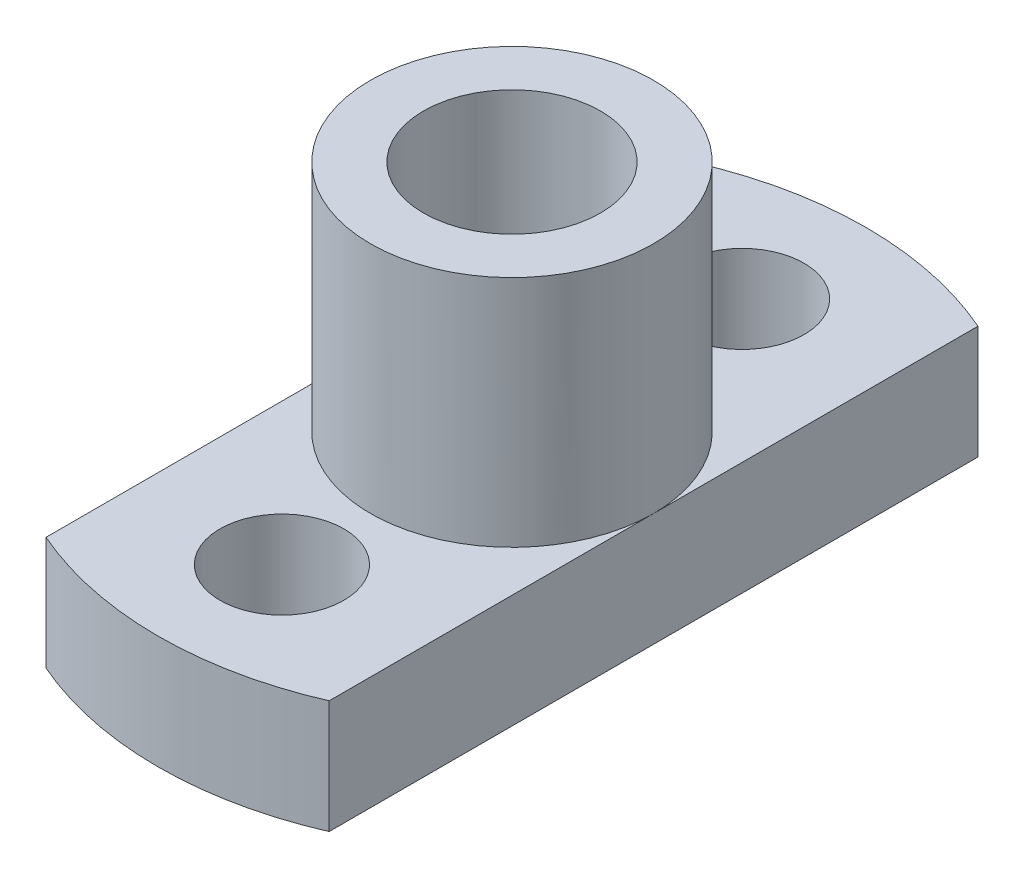
SolidWorks part; units mm, degrees
ref_plane "前视基准面" through (0, 0, 0) normal (0, 0, 1) x (1, 0, 0)
ref_plane "上视基准面" through (0, 0, 0) normal (0, 1, 0) x (1, 0, 0)
ref_plane "右视基准面" through (0, 0, 0) normal (1, 0, 0) x (0, 0, -1)
sketch "草图2" plane through (0, 0, 0) normal (0, 1, 0) x (1, 0, 0)
  line L0 (0, 10) -> (0, -10) construction
  line L1 (-4, 9.1652) -> (-4, -9.1652)
  line L2 (4, 9.1652) -> (4, -9.1652)
  line L3 (-4, 0) -> (4, 0) construction
  arc A0 (-4, -9.1652) -> (4, -9.1652) centre (0, 0) ccw
  arc A1 (4, 9.1652) -> (-4, 9.1652) centre (0, 0) ccw
  circle A3 centre (0, 6.5) radius 1.75
  circle A4 centre (0, -6.5) radius 1.75
  dimension "D1" = 20
  dimension "D3" = 3.5
  dimension "D2" = 8
  dimension "D4" = 13
extrude "凸台-拉伸1" add sketch "草图2" along normal blind 3.2
sketch "草图3" plane through (0, 3.2, 0) normal (0, 1, 0) x (1, 0, 0)
  circle A0 centre (0, 0) radius 4
  dimension "D1" = 8
extrude "凸台-拉伸2" add sketch "草图3" along normal blind 6.6
sketch "草图4" plane through (0, 9.8, 0) normal (0, 1, 0) x (1, 0, 0)
  circle A0 centre (0, 0) radius 2.5
  dimension "D1" = 5
extrude "切除-拉伸1" cut sketch "草图4" against normal through all
